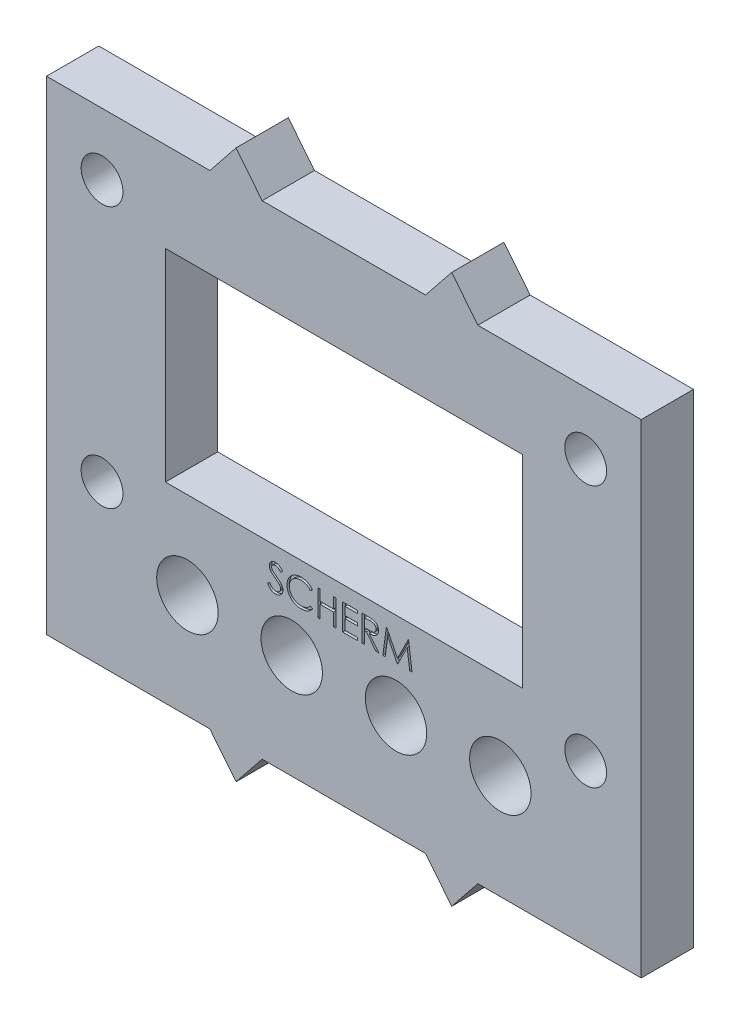
SolidWorks part; units mm, degrees
ref_plane "Front Plane" through (0, 0, 0) normal (0, 0, 1) x (1, 0, 0)
ref_plane "Top Plane" through (0, 0, 0) normal (0, 1, 0) x (1, 0, 0)
ref_plane "Right Plane" through (0, 0, 0) normal (1, 0, 0) x (0, 0, -1)
sketch "Sketch1" plane through (0, 0, 0) normal (0, 0, 1) x (1, 0, 0)
  line L0 (22.75, 37) -> (22.75, 14.7203) construction
  line L1 (0, 0) -> (45.5, 0)
  line L2 (0, 0) -> (0, 37)
  line L3 (0, 37) -> (45.5, 37)
  line L4 (45.5, 0) -> (45.5, 37)
  line L5 (12.5, 37) -> (14.5, 39.5)
  line L6 (14.5, 39.5) -> (16.5, 37)
  line L7 (31, 39.5) -> (29, 37)
  line L8 (33, 37) -> (31, 39.5)
  line L9 (0, 18.5) -> (57.9593, 18.5) construction
  line L10 (33, 0) -> (31, -2.5)
  line L11 (31, -2.5) -> (29, 0)
  line L12 (14.5, -2.5) -> (16.5, 0)
  line L13 (12.5, 0) -> (14.5, -2.5)
  point P9 (22.75, 37)
  point P16 (0, 18.5)
  point P17 (32, 38.25)
  point P18 (32, -1.25)
  dimension "D1" = 37
  dimension "D2" = 45.5
  dimension "D3" = 16.5
  dimension "D4" = 2.5
  dimension "D5" = 4
extrude "Basis" add sketch "Sketch1" along normal blind 4 contours L1 L4 L3 L2 | L6 L5 L3 | L3 L8 L7 | L1 L13 L12 | L11 L10 L1
sketch "Sketch2" [suppressed] plane through (0, 0, 4) normal (0, 0, 1) x (1, 0, 0)
  line L0 (16.5, 37) -> (29, 37) construction
  circle A0 centre (22.75, 23) radius 6.8
  point P5 (22.75, 37)
  dimension "D1" = 13.6
  dimension "D2" = 14
extrude "Camera gat " [suppressed] cut sketch "Sketch2" against normal up to surface (4 mm away)
sketch "Sketch5" [suppressed] plane through (0, 0, 4) normal (0, 0, 1) x (1, 0, 0)
  line L0 (8.6574, 7.1957) -> (36.8426, 7.1957) construction
  line L1 (16.5, 37) -> (29, 37) construction
  text T0 "camera" font "Bebas Kai" height 3.5
  point P2 (22.75, 7.1957)
  point P5 (22.75, 37)
extrude "Cut-Extrude4" [suppressed] cut sketch "Sketch5" against normal blind 0.2
sketch "Sketch3" [suppressed] plane through (0, 0, 4) normal (0, 0, 1) x (1, 0, 0)
  line L0 (22.75, 37) -> (22.75, 0) construction
  line L1 (16.5, 37) -> (29, 37) construction
  line L2 (16.5, 0) -> (29, 0) construction
  line L3 (0, 37) -> (12.5, 37) construction
  circle A0 centre (9.8, 25.6) radius 7.95
  circle A1 centre (35.7, 25.6) radius 7.95
  dimension "D3" = 15.9
  dimension "D1" = 11.4
  dimension "D2" = 25.9
extrude "HR04 gat " [suppressed] cut sketch "Sketch3" against normal up to surface (4 mm away)
sketch "Sketch4" [suppressed] plane through (0, 0, 4) normal (0, 0, 1) x (1, 0, 0)
  line L0 (7.7992, 12.9938) -> (37.7008, 12.9938) construction
  line L1 (16.5, 37) -> (29, 37) construction
  text T0 "AFSTAND SENSOR" font "Bebas Kai" height 3.5
  point P5 (22.75, 12.9938)
  point P8 (22.75, 37)
extrude "Afstand sensor" [suppressed] cut sketch "Sketch4" against normal blind 0.2
sketch "Sketch10" plane through (0, 0, 4) normal (0, 0, 1) x (1, 0, 0)
  line L1 (17.42, 29.57) -> (28.08, 29.57)
  line L2 (17.42, 29.57) -> (17.42, 34.43)
  line L3 (17.42, 34.43) -> (28.08, 34.43)
  line L4 (28.08, 29.57) -> (28.08, 34.43)
  line L5 (17.42, 29.57) -> (28.08, 34.43) construction
  line L6 (17.42, 34.43) -> (28.08, 29.57) construction
  line L9 (16.5, 37) -> (29, 37) construction
  point P4 (22.75, 32)
  point P5 (22.75, 37)
  point P6 (22.75, 34.43)
  dimension "D1" = 4.86
  dimension "D2" = 10.66
  dimension "D3" = 32
extrude "Press_fit" [suppressed] cut sketch "Sketch10" against normal blind 10
sketch "Sketch6" plane through (0, 0, 4) normal (0, 0, 1) x (1, 0, 0)
  line L4 (16.5, 37) -> (29, 37) construction
  point P0 (22.75, 30.14)
  point P3 (22.75, 37)
  line B0 (9.1, 30.14) -> (36.4, 30.14)
  line B1 (9.1, 30.14) -> (9.1, 14.6591)
  line B2 (9.1, 14.6591) -> (36.4, 14.6591)
  line B3 (36.4, 30.14) -> (36.4, 14.6591)
  circle B4 centre (11.1, 32.4381) radius 1.5
  circle B5 centre (34.4, 32.4381) radius 1.5
  circle B6 centre (34.4, 8.6381) radius 1.5
  circle B7 centre (11.1, 8.6381) radius 1.5
  dimension "D1" = 6.86
sketch_block_instance "Block1-1" [suppressed]
sketch_block "Block1" parameters "D1"=3, "D2"=3, "D3"=3, "D4"=3
extrude "Show only screen" cut sketch "Sketch6" against normal blind 10.04 contours B3 B0 B1 B2
sketch "Sketch7" [suppressed] plane through (0, 0, 4) normal (0, 0, 1) x (1, 0, 0)
  line L0 (-2.0092, 11.0348) -> (47.5092, 11.0348) construction
  line L1 (16.5, 37) -> (29, 37) construction
  text T0 "oled scherm " font "Bebas Kai" height 3.5
  point P4 (22.75, 37)
  point P5 (22.75, 11.0348)
extrude "Cut-Extrude6" [suppressed] cut sketch "Sketch7" against normal blind 0.2
sketch "Sketch9" plane through (0, 0, 4) normal (0, 0, 1) x (1, 0, 0)
  line L0 (16.8642, 11.5) -> (28.6358, 11.5) construction
  line L1 (16.5, 0) -> (29, 0) construction
  text T0 "SCHERM" font "Century Gothic" height 2
  point P8 (22.75, 0)
  point P9 (22.75, 11.5)
  dimension "D1" = 11.5
sketch "Sketch11" plane through (0, 0, 0) normal (0, 0, -1) x (-1, 0, 0)
  line L0 (0, 0) -> (-45.5, 0) construction
  line L1 (-41.25, 32.2526) -> (-4.25, 32.2526) construction
  line L2 (-41.25, 32.2526) -> (-41.25, 12.2526) construction
  line L3 (-41.25, 12.2526) -> (-4.25, 12.2526) construction
  line L4 (-4.25, 32.2526) -> (-4.25, 12.2526) construction
  circle A0 centre (-41.25, 32.2526) radius 1.6
  circle A1 centre (-4.25, 32.2526) radius 1.6
  circle A2 centre (-4.25, 12.2526) radius 1.6
  circle A3 centre (-41.25, 12.2526) radius 1.6
  point P6 (-22.75, 12.2526)
  point P7 (-22.75, 0)
  dimension "D1" = 3.2
  dimension "D3" = 12.2526
  dimension "D4" = 20
  dimension "D5" = 37
extrude "Cut-Extrude10" cut sketch "Sketch11" against normal blind 4
sketch "Sketch12" plane through (0, 0, 0) normal (0, 0, -1) x (-1, 0, 0)
  line L0 (0, 0) -> (0, 8) construction
  line L1 (0, 0) -> (0, 37) construction
  line L2 (-45.5, 8) -> (-34.72, 8) construction
  line L3 (-18.76, 8) -> (-10.78, 8) construction
  line L4 (-45.5, 0) -> (-45.5, 37) construction
  line L5 (-34.72, 8) -> (-26.74, 8) construction
  line L7 (-26.74, 8) -> (-18.76, 8) construction
  line L8 (-10.78, 8) -> (0, 8) construction
  circle A4 centre (-34.72, 8) radius 2.35
  circle A7 centre (-18.76, 8) radius 2.35
  circle A8 centre (-26.74, 8) radius 2.35
  circle A9 centre (-10.78, 8) radius 2.35
  dimension "D2" = 4.7
  dimension "D1" = 7.98
  dimension "D3" = 8
extrude "Lego gaten" cut sketch "Sketch12" against normal blind 10
extrude "Cut-Extrude11" cut sketch "Sketch9" against normal blind 0.2
